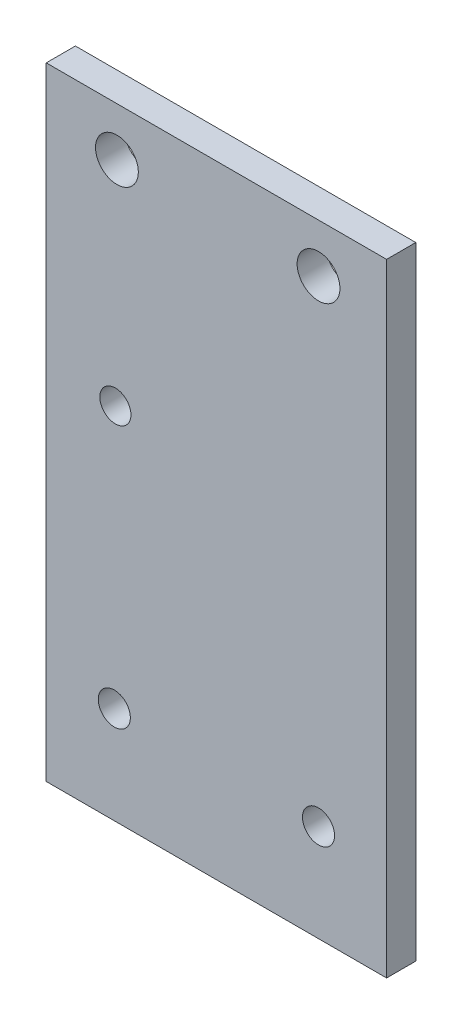
SolidWorks part; units mm, degrees
ref_plane "正面" through (0, 0, 0) normal (0, 0, 1) x (1, 0, 0)
ref_plane "平面" through (0, 0, 0) normal (0, 1, 0) x (1, 0, 0)
ref_plane "右側面" through (0, 0, 0) normal (1, 0, 0) x (0, 0, -1)
sketch "ｽｹｯﾁ1" plane through (0, 0, 0) normal (0, 0, 1) x (1, 0, 0)
  line L1 (-20, 14.5) -> (20, 14.5)
  line L2 (-20, 14.5) -> (-20, -14.5)
  line L3 (-20, -14.5) -> (20, -14.5)
  line L4 (20, 14.5) -> (20, -14.5)
  line L5 (-20, 14.5) -> (20, -14.5) construction
  line L6 (-20, -14.5) -> (20, 14.5) construction
  point P0 (0, 0)
  dimension "D1" = 40
  dimension "D2" = 29
extrude "ﾎﾞｽ - 押し出し1" add sketch "ｽｹｯﾁ1" along normal blind 3
sketch "ｽｹｯﾁ2" plane through (0, 0, 3) normal (0, 0, 1) x (1, 0, 0)
  line L1 (-20, 14.5) -> (-16.5, 14.5)
  line L2 (-20, 14.5) -> (-20, 10.5)
  line L3 (-20, 10.5) -> (-16.5, 10.5)
  line L4 (-16.5, 14.5) -> (-16.5, 10.5)
  line L5 (-20, -14.5) -> (-16.5, -14.5)
  line L6 (-20, -14.5) -> (-20, -10.5)
  line L7 (-20, -10.5) -> (-16.5, -10.5)
  line L8 (-16.5, -14.5) -> (-16.5, -10.5)
  line L9 (20, -14.5) -> (16.5, -14.5)
  line L10 (20, -14.5) -> (20, -10.5)
  line L11 (20, -10.5) -> (16.5, -10.5)
  line L12 (16.5, -14.5) -> (16.5, -10.5)
  line L13 (20, 14.5) -> (16.5, 14.5)
  line L14 (20, 14.5) -> (20, 10.5)
  line L15 (20, 10.5) -> (16.5, 10.5)
  line L16 (16.5, 14.5) -> (16.5, 10.5)
  circle A0 centre (-16.5, 10.5) radius 2.1
  circle A1 centre (-16.5, -10.5) radius 2.1
  circle A2 centre (16.5, -10.5) radius 2.1
  circle A3 centre (16.5, 10.5) radius 2.1
  dimension "D9" = 4.2
  dimension "D10" = 4.2
  dimension "D11" = 4.2
  dimension "D12" = 4.2
  dimension "D1" = 3.5
  dimension "D2" = 4
  dimension "D3" = 3.5
  dimension "D4" = 4
  dimension "D5" = 3.5
  dimension "D6" = 4
  dimension "D7" = 3.5
  dimension "D8" = 4
extrude "ｶｯﾄ - 押し出し1" cut sketch "ｽｹｯﾁ2" against normal blind 3 contours L3 A0 L4 | L4 A0 L3 | L8 A1 L7 | L7 A1 L8 | L12 A2 L11 | L11 A2 L12 | L16 A3 L15 | L15 A3 L16
sketch "ｽｹｯﾁ3" plane through (0, -14.5, 0) normal (0, -1, 0) x (1, 0, 0)
  line L1 (20, 0) -> (-20, 0)
  line L2 (20, 0) -> (20, 3)
  line L3 (20, 3) -> (-20, 3)
  line L4 (-20, 0) -> (-20, 3)
extrude "ﾎﾞｽ - 押し出し2" add sketch "ｽｹｯﾁ3" along normal blind 10
sketch "ｽｹｯﾁ4" plane through (0, 14.5, 0) normal (0, 1, 0) x (1, 0, 0)
  line L1 (20, -3) -> (-20, -3)
  line L2 (20, -3) -> (20, 0)
  line L3 (20, 0) -> (-20, 0)
  line L4 (-20, -3) -> (-20, 0)
extrude "ﾎﾞｽ - 押し出し3" add sketch "ｽｹｯﾁ4" along normal blind 10
sketch "ｽｹｯﾁ6" plane through (20, 0, 0) normal (1, 0, 0) x (0, 0, -1)
  line L1 (0, 24.5) -> (-3, 24.5)
  line L2 (0, 24.5) -> (0, -24.5)
  line L3 (0, -24.5) -> (-3, -24.5)
  line L4 (-3, 24.5) -> (-3, -24.5)
extrude "ﾎﾞｽ - 押し出し5" add sketch "ｽｹｯﾁ6" along normal blind 42
sketch "ｽｹｯﾁ7" plane through (0, 0, 3) normal (0, 0, 1) x (1, 0, 0)
  line L0 (62, 0) -> (43.1058, 0)
  line L1 (62, 24.5) -> (62, -24.5) construction
  line L2 (43.1058, 0) -> (36.1058, 0)
  line L7 (31.9689, -11.1369) -> (54.2427, 11.1369) construction
  line L8 (31.9689, 11.1369) -> (54.2427, -11.1369) construction
  line L9 (43.1058, 0) -> (29.4659, 7.875)
  line L10 (43.1058, 0) -> (43.1058, 15.75)
  line L11 (43.1058, 0) -> (56.7457, 7.875)
  line L12 (43.1058, 0) -> (29.4659, -7.875)
  line L13 (43.1058, 0) -> (43.1058, -15.75)
  line L14 (43.1058, 0) -> (56.7457, -7.875)
  circle A0 centre (43.1058, 0) radius 15.75
  circle A6 centre (43.1058, 15.75) radius 1.75
  circle A7 centre (29.4659, -7.875) radius 1.75
  circle A8 centre (43.1058, -15.75) radius 1.75
  circle A9 centre (56.7457, -7.875) radius 1.75
  circle A10 centre (56.7457, 7.875) radius 1.75
  circle A11 centre (36.1058, 0) radius 7
  dimension "D3" = 60
  dimension "D4" = 7
  dimension "D5" = 60
  dimension "D6" = 60
  dimension "D7" = 31.5
  dimension "D9" = 3.5
  dimension "D10" = 3.5
  dimension "D11" = 3.5
  dimension "D12" = 3.5
  dimension "D13" = 3.5
  dimension "D14" = 14
  dimension "D2" = 60
sketch "ｽｹｯﾁ8" plane through (-20, 0, 0) normal (-1, 0, 0) x (0, 0, 1)
  line L1 (3, -24.5) -> (0, -24.5)
  line L2 (3, -24.5) -> (3, 24.5)
  line L3 (3, 24.5) -> (0, 24.5)
  line L4 (0, -24.5) -> (0, 24.5)
extrude "ﾎﾞｽ - 押し出し6" add sketch "ｽｹｯﾁ8" along normal blind 2
sketch "ｽｹｯﾁ9" plane through (62, 0, 0) normal (1, 0, 0) x (0, 0, -1)
  line L1 (0, 24.5) -> (-3, 24.5)
  line L2 (0, 24.5) -> (0, -24.5)
  line L3 (0, -24.5) -> (-3, -24.5)
  line L4 (-3, 24.5) -> (-3, -24.5)
extrude "ﾎﾞｽ - 押し出し7" add sketch "ｽｹｯﾁ9" along normal blind 2
sketch "ｽｹｯﾁ10" plane through (0, -24.5, 0) normal (0, -1, 0) x (1, 0, 0)
  line L1 (-22, 0) -> (64, 0)
  line L2 (-22, 0) -> (-22, 3)
  line L3 (-22, 3) -> (64, 3)
  line L4 (64, 0) -> (64, 3)
extrude "ﾎﾞｽ - 押し出し8" add sketch "ｽｹｯﾁ10" along normal blind 10
sketch "ｽｹｯﾁ11" plane through (0, 24.5, 0) normal (0, 1, 0) x (1, 0, 0)
  line L1 (-22, 0) -> (64, 0)
  line L2 (-22, 0) -> (-22, -3)
  line L3 (-22, -3) -> (64, -3)
  line L4 (64, 0) -> (64, -3)
extrude "ﾎﾞｽ - 押し出し9" add sketch "ｽｹｯﾁ11" along normal blind 10
sketch "ｽｹｯﾁ14" plane through (-22, 0, 0) normal (-1, 0, 0) x (0, 0, 1)
  line L0 (0, 34.5) -> (0, -34.5) construction
  line L1 (3, -34.5) -> (0, -34.5)
  line L2 (3, -34.5) -> (3, 34.5)
  line L3 (3, 34.5) -> (0, 34.5)
  line L4 (0, -34.5) -> (0, 34.5)
  line L5 (0, 34.5) -> (3, 34.5) construction
extrude "ｶｯﾄ - 押し出し5" cut sketch "ｽｹｯﾁ14" against normal blind 43
sketch "ｽｹｯﾁ17" plane through (0, -34.5, 0) normal (0, -1, 0) x (1, 0, 0)
  line L1 (21, 3) -> (64, 3)
  line L2 (21, 3) -> (21, 0)
  line L3 (21, 0) -> (64, 0)
  line L4 (64, 3) -> (64, 0)
extrude "ﾎﾞｽ - 押し出し10" add sketch "ｽｹｯﾁ17" along normal blind 20
sketch "ｽｹｯﾁ18" plane through (0, 0, 3) normal (0, 0, 1) x (1, 0, 0)
  line L0 (21, -54.5) -> (21, -34.5)
  line L1 (21, -54.5) -> (21, 34.5) construction
  line L3 (64, -54.5) -> (64, -34.5)
  line L4 (64, 34.5) -> (64, -54.5) construction
  line L5 (64, -34.5) -> (57, -34.5)
  line L6 (21, -34.5) -> (36, -34.5)
  circle A0 centre (36, -34.5) radius 1
  circle A1 centre (57, -34.5) radius 1
  dimension "D5" = 2
  dimension "D6" = 2
  dimension "D1" = 20
  dimension "D2" = 20
  dimension "D3" = 7
  dimension "D4" = 15
sketch "ｽｹｯﾁ19" plane through (0, 0, 3) normal (0, 0, 1) x (1, 0, 0)
  line L0 (42.5, -54.5) -> (42.5, 34.5)
  line L1 (64, -54.5) -> (21, -54.5) construction
  line L2 (21, 34.5) -> (64, 34.5) construction
  circle A0 centre (36, -34.5) radius 1 construction
  circle A1 centre (57, -34.5) radius 1 construction
  dimension "D2" = 14.5
  dimension "D1" = 6.5
sketch "ｽｹｯﾁ20" plane through (0, -54.5, 0) normal (0, -1, 0) x (1, 0, 0)
  line L1 (64, 0) -> (21, 0)
  line L2 (64, 0) -> (64, 3)
  line L3 (64, 3) -> (21, 3)
  line L4 (21, 0) -> (21, 3)
extrude "ﾎﾞｽ - 押し出し11" add sketch "ｽｹｯﾁ20" along normal blind 10
sketch "ｽｹｯﾁ21" plane through (0, -64.5, 0) normal (0, -1, 0) x (1, 0, 0)
  line L1 (21, 3) -> (64, 3)
  line L2 (21, 3) -> (21, 0)
  line L3 (21, 0) -> (64, 0)
  line L4 (64, 3) -> (64, 0)
extrude "ｶｯﾄ - 押し出し7" cut sketch "ｽｹｯﾁ21" against normal blind 20
sketch "ｽｹｯﾁ22" plane through (0, 0, 3) normal (0, 0, 1) x (1, 0, 0)
  circle A0 centre (29.4659, 7.875) radius 1.75
sketch "ｽｹｯﾁ24" plane through (0, 0, 0) normal (0, 0, -1) x (-1, 0, 0)
  line L0 (-42.5, 34.5) -> (-36.27, 34.5)
  line L1 (-64, 34.5) -> (-21, 34.5) construction
  line L2 (-36.27, 34.5) -> (-36.27, 14.5)
  line L3 (-64, 34.5) -> (-64, 14.5)
  line L4 (-64, -44.5) -> (-64, 34.5) construction
  line L5 (-64, 14.5) -> (-57, 14.5)
  circle A0 centre (-36.27, 14.5) radius 2.2
  circle A1 centre (-57, 14.5) radius 2.2
  dimension "D6" = 4.4
  dimension "D7" = 4.4
  dimension "D1" = 6.23
  dimension "D2" = 20
  dimension "D3" = 20
  dimension "D4" = 0
  dimension "D5" = 7
extrude "ｶｯﾄ - 押し出し8" cut sketch "ｽｹｯﾁ24" against normal blind 30
sketch "ｽｹｯﾁ25" plane through (0, 0, 0) normal (0, 0, -1) x (-1, 0, 0)
  line L0 (-21, 34.5) -> (-21, 31.5)
  line L1 (-21, 34.5) -> (-21, -44.5) construction
  line L2 (-21, 31.5) -> (-24, 31.5)
  line L3 (-24, 31.5) -> (-24, 16.9055)
  line L4 (-24, 16.9055) -> (-46.2, 16.9055)
  line L5 (-46.2, 16.9055) -> (-46.2, 27.2055)
  circle A0 centre (-24, 16.9055) radius 1.55
  circle A1 centre (-46.2, 27.2055) radius 1.55
  dimension "D5" = 3.1
  dimension "D6" = 3.1
  dimension "D1" = 3
  dimension "D2" = 3
  dimension "D3" = 22.2
  dimension "D4" = 10.3
sketch "ｽｹｯﾁ26" plane through (0, 0, 0) normal (0, 0, -1) x (-1, 0, 0)
  line L0 (-42.5, -44.5) -> (-36.11, -44.5)
  line L2 (-21, -44.5) -> (-64, -44.5) construction
  line L3 (-36.11, -44.5) -> (-36.11, -7.5)
  circle A1 centre (-36.11, -7.5) radius 1.6
  dimension "D3" = 3.2
  dimension "D1" = 6.39
  dimension "D2" = 37
extrude "ｶｯﾄ - 押し出し9" cut sketch "ｽｹｯﾁ26" against normal blind 10
sketch "ｽｹｯﾁ27" plane through (21, 0, 0) normal (-1, 0, 0) x (0, 0, 1)
  line L1 (0, 34.5) -> (3, 34.5)
  line L2 (0, 34.5) -> (0, -44.5)
  line L3 (0, -44.5) -> (3, -44.5)
  line L4 (3, 34.5) -> (3, -44.5)
extrude "ｶｯﾄ - 押し出し10" cut sketch "ｽｹｯﾁ27" against normal blind 8
sketch "ｽｹｯﾁ28" plane through (0, 34.5, 0) normal (0, 1, 0) x (1, 0, 0)
  line L1 (29, -3) -> (64, -3)
  line L2 (29, -3) -> (29, 0)
  line L3 (29, 0) -> (64, 0)
  line L4 (64, -3) -> (64, 0)
extrude "ｶｯﾄ - 押し出し11" cut sketch "ｽｹｯﾁ28" against normal blind 15
sketch "ｽｹｯﾁ33" plane through (0, 0, 0) normal (0, 0, -1) x (-1, 0, 0)
  line L1 (-29, -44.5) -> (-36, -44.5)
  line L2 (-29, -44.5) -> (-29, -34.5)
  line L3 (-29, -34.5) -> (-36, -34.5)
  line L4 (-36, -44.5) -> (-36, -34.5)
  line L5 (-64, -44.5) -> (-57, -44.5)
  line L6 (-64, -44.5) -> (-64, -34.5)
  line L7 (-64, -34.5) -> (-57, -34.5)
  line L8 (-57, -44.5) -> (-57, -34.5)
  circle A0 centre (-36, -34.5) radius 1
  circle A1 centre (-57, -34.5) radius 1
  dimension "D5" = 2
  dimension "D6" = 2
  dimension "D1" = 7
  dimension "D2" = 7
  dimension "D3" = 10
  dimension "D4" = 10
extrude "ｶｯﾄ - 押し出し13" cut sketch "ｽｹｯﾁ33" against normal blind 10 contours L3 A0 L4 | L4 A0 L3 | L8 A1 L7 | L7 A1 L8
hole_wizard "M4x0.7 ねじ穴3" positions "3Dｽｹｯﾁ4" profile "ｽｹｯﾁ34" tap size "M4x0.7" standard "JIS" end condition through all
sketch3d "3Dｽｹｯﾁ4"
  line L0 (36, -34.5, 3) -> (36, -34.5, 0) construction
  line L1 (57, -34.5, 3) -> (57, -34.5, 0) construction
  point P0 (36, -34.5, 0)
  point P4 (57, -34.5, 0)
sketch "ｽｹｯﾁ34" plane through (36, -34.5, 0) normal (1, 0, 0) x (0, 1, 0)
  line L0 (0, 0) -> (0, 3)
  line L1 (0, 3) -> (1.65, 3)
  line L2 (1.65, 3) -> (1.65, 0)
  line L5 (1.65, 0) -> (0, 0)
  line L11 (0, -6.35) -> (0, 107.95) construction
  dimension "次ｻｰﾌｪｽまでのねじ下穴ﾄﾞﾘﾙ直径" = 3.3
  dimension "次ｻｰﾌｪｽまでのねじ下穴ﾄﾞﾘﾙの深さ" = 3
cosmetic thread "穴のねじ山5" parameters "D2"=4
cosmetic thread "穴のねじ山6" parameters "D2"=4
